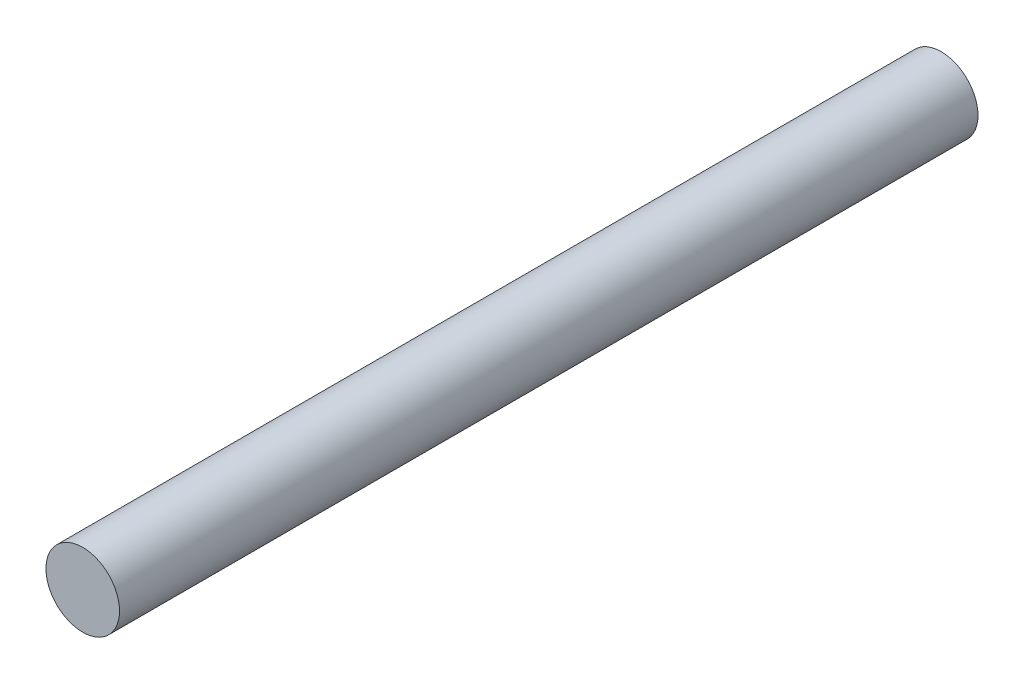
SolidWorks part; units mm, degrees
ref_plane "Front Plane" through (0, 0, 0) normal (0, 0, 1) x (1, 0, 0)
ref_plane "Top Plane" through (0, 0, 0) normal (0, 1, 0) x (1, 0, 0)
ref_plane "Right Plane" through (0, 0, 0) normal (1, 0, 0) x (0, 0, -1)
sketch "Sketch2" plane through (0, 0, 0) normal (0, 0, 1) x (1, 0, 0)
  circle A0 centre (0, 0) radius 1.5
extrude "Boss-Extrude1" add sketch "Sketch2" along normal blind 35
